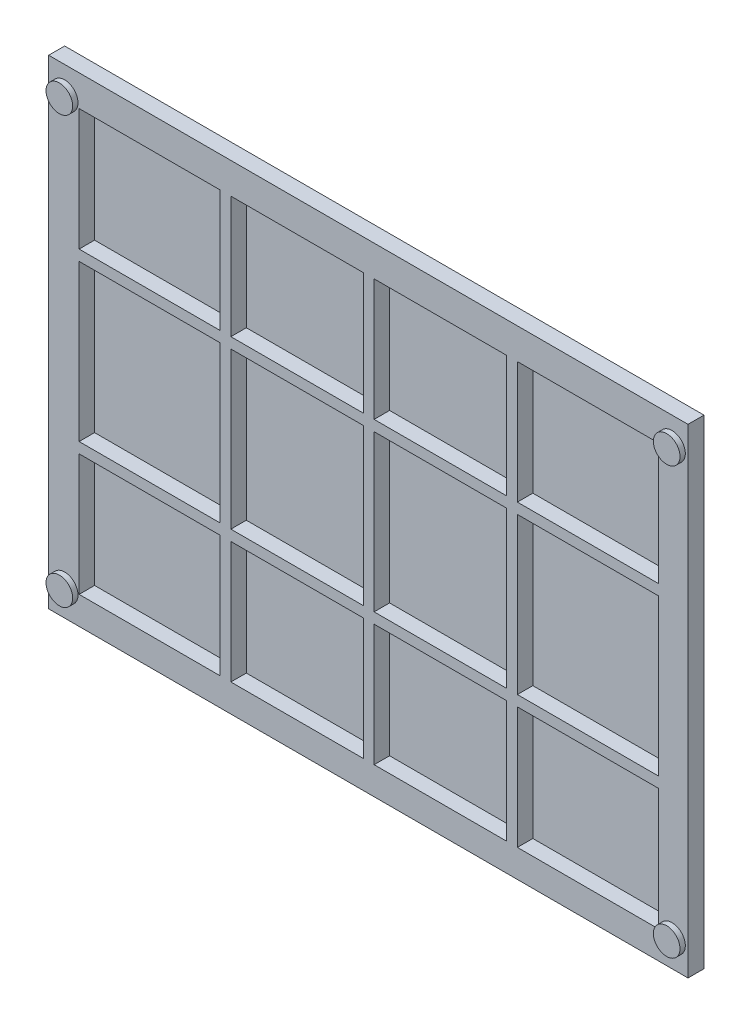
SolidWorks part; units mm, degrees
material "6061 Alloy"
ref_plane "Front Plane" through (0, 0, 0) normal (0, 0, 1) x (1, 0, 0)
ref_plane "Top Plane" through (0, 0, 0) normal (0, 1, 0) x (1, 0, 0)
ref_plane "Right Plane" through (0, 0, 0) normal (1, 0, 0) x (0, 0, -1)
sketch "Sketch2" plane through (0, 0, 0) normal (0, 0, 1) x (1, 0, 0)
  line L1 (0, 0) -> (1200, 0)
  line L2 (0, 0) -> (0, 900)
  line L3 (0, 900) -> (1200, 900)
  line L4 (1200, 0) -> (1200, 900)
  dimension "D1" = 900
  dimension "D2" = 1200
extrude "Boss-Extrude2" add sketch "Sketch2" along normal blind 30 contours L1 L4 L3 L2
sketch "Sketch3" plane through (0, 0, 30) normal (0, 0, 1) x (1, 0, 0)
  line L1 (57.1339, 841.9291) -> (1144.5573, 841.9291)
  line L2 (57.1339, 841.9291) -> (57.1339, 52.1518)
  line L3 (57.1339, 52.1518) -> (1144.5573, 52.1518)
  line L4 (1144.5573, 841.9291) -> (1144.5573, 52.1518)
extrude "Cut-Extrude2" cut sketch "Sketch3" against normal blind 29 contours L2 L3 L4 L1
sketch "Sketch6" plane through (0, 0, 30) normal (0, 0, 1) x (1, 0, 0)
  line L0 (600.8456, 841.9291) -> (600.8456, 52.1518)
  line L1 (57.1339, 841.9291) -> (1144.5573, 841.9291) construction
  line L2 (57.1339, 52.1518) -> (1144.5573, 52.1518) construction
  line L3 (331.9493, 841.9291) -> (331.9493, 52.1518)
  line L4 (57.1339, 603.4738) -> (1144.5573, 603.4738)
  line L5 (869.7419, 841.9291) -> (869.7419, 52.1518)
  line L6 (57.1339, 841.9291) -> (57.1339, 52.1518) construction
  line L7 (1144.5573, 841.9291) -> (1144.5573, 52.1518) construction
  line L8 (57.1339, 290.6071) -> (1144.5573, 290.6071)
rib "Rib6" sketch "Sketch6" sketch "Sketch6" thickness 20 extrusion direction normal to sketch draft on no parameters "D1"=20
sketch "Sketch7" plane through (0, 0, 30) normal (0, 0, 1) x (1, 0, 0)
  line L0 (600, 900) -> (600, 0)
  line L1 (0, 900) -> (1200, 900) construction
  line L2 (0, 0) -> (1200, 0) construction
  line L3 (0, 450) -> (1200, 450)
  line L4 (0, 0) -> (0, 900) construction
  line L5 (1200, 0) -> (1200, 900) construction
  circle A0 centre (30, 850) radius 25
  circle A1 centre (30, 50) radius 25
  circle A2 centre (1170, 50) radius 25
  circle A3 centre (1170, 850) radius 25
  dimension "D1" = 50
  dimension "D2" = 400
  dimension "D3" = 570
extrude "Boss-Extrude3" add sketch "Sketch7" along normal blind 10 contours A1 | A0 | A2 | A3
